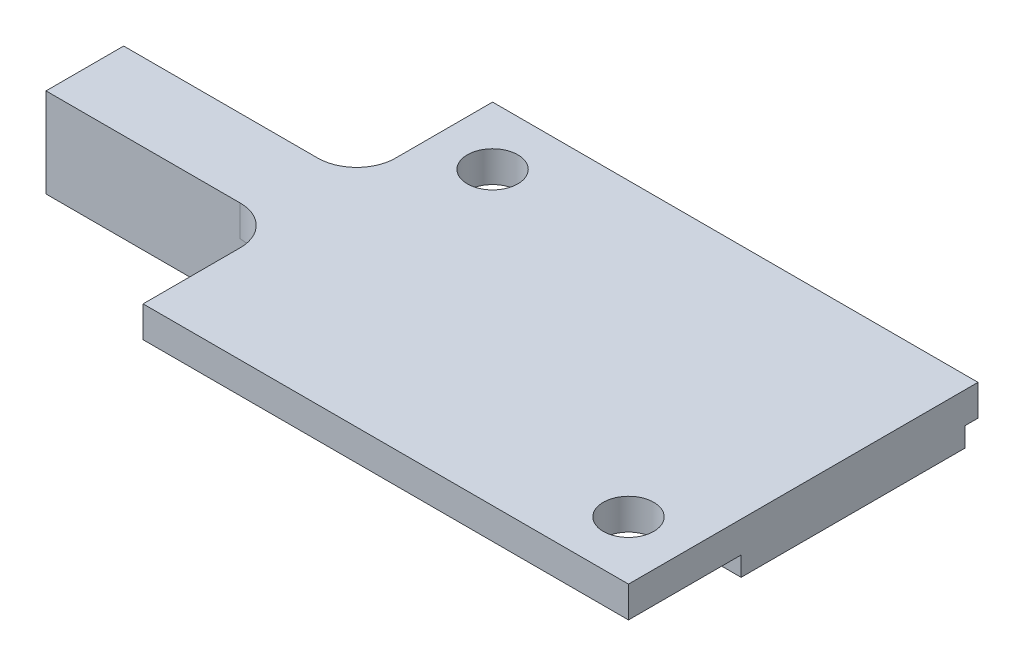
SolidWorks part; units mm, degrees
material "ABS"
ref_plane "Front Plane" through (0, 0, 0) normal (0, 0, 1) x (1, 0, 0)
ref_plane "Top Plane" through (0, 0, 0) normal (0, 1, 0) x (1, 0, 0)
ref_plane "Right Plane" through (0, 0, 0) normal (1, 0, 0) x (0, 0, -1)
sketch "Sketch1" plane through (0, 0, 0) normal (0, 1, 0) x (1, 0, 0)
  line L0 (0, 11) -> (0, 18)
  line L1 (0, 0) -> (25, 0)
  line L2 (0, 0) -> (0, 7)
  line L3 (0, 18) -> (25, 18)
  line L4 (25, 0) -> (25, 18)
  line L5 (0, 7) -> (-12, 7)
  line L7 (0, 11) -> (-12, 11)
  line L8 (-12, 7) -> (-12, 11)
  dimension "D1" = 18
  dimension "D2" = 25
  dimension "D3" = 4
  dimension "D4" = 12
  dimension "D5" = 7
extrude "Boss-Extrude1" add sketch "Sketch1" along normal blind 1.6
sketch "Sketch2" plane through (-12, 0, 0) normal (-1, 0, 0) x (0, 0, 1)
  line L0 (-9, 1.6) -> (-9, -4.9854) construction
  line L1 (-11, 1.6) -> (-7, 1.6) construction
  line L2 (-11, 0) -> (-7, 0) construction
  line L4 (-7, -3) -> (-7, 0)
  line L5 (-11, -3) -> (-11, 0)
  line L6 (-7, 0) -> (-11, 0)
  arc A0 (-7, -3) -> (-11, -3) centre (-9, -3) ccw
  line M1 (-11, 0) -> (-7, 0)
  dimension "D1" = 4
  dimension "D2" = 3
extrude "Boss-Extrude2" add sketch "Sketch2" against normal up to surface (12 mm away) contours A0 L4 L6 | A0 L5 M1 up to face at (0, 0.8, -14.5)
sketch "Sketch3" plane through (0, 1.6, 0) normal (0, 1, 0) x (1, 0, 0)
  line L0 (0, 18) -> (0, 11) construction
  line L1 (25, 18) -> (0, 18) construction
  line L2 (25, 0) -> (25, 18) construction
  line L3 (0, 0) -> (25, 0) construction
  circle A0 centre (3, 15) radius 1.3
  circle A1 centre (22, 3) radius 1.3
  dimension "D1" = 2.6
  dimension "D2" = 2.6
  dimension "D3" = 3
  dimension "D4" = 3
  dimension "D5" = 3
  dimension "D6" = 3
extrude "Cut-Extrude1" cut sketch "Sketch3" against normal blind 1.6
fillet "Fillet1" radius 2 2 edges at (0, 0.8, -7) (0, 0.8, -11)
sketch "Sketch4" plane through (0, 0, 0) normal (0, -1, 0) x (1, 0, 0)
  line L0 (-12, -9) -> (28.8588, -9) construction
  line L1 (-12, -7) -> (-12, -11) construction
  line L2 (25, -5.8) -> (25, -17.33)
  line L3 (25, 0) -> (25, -18) construction
  line L4 (25, -17.33) -> (20.2856, -15.0198)
  line L5 (20.2856, -15.0198) -> (23, -11.947)
  line L6 (23, -11.947) -> (23, -5.8)
  line L7 (23, -5.8) -> (25, -5.8)
  line L8 (25, -18) -> (0, -18) construction
  dimension "D1" = 2
  dimension "D2" = 11.53
  dimension "D3" = 5.25
  dimension "D4" = 4.1
  dimension "D5" = 74.65
  dimension "D6" = 0.67
extrude "Boss-Extrude3" add sketch "Sketch4" along normal blind 1
equation "\"ˇ2\"=1.45231"
